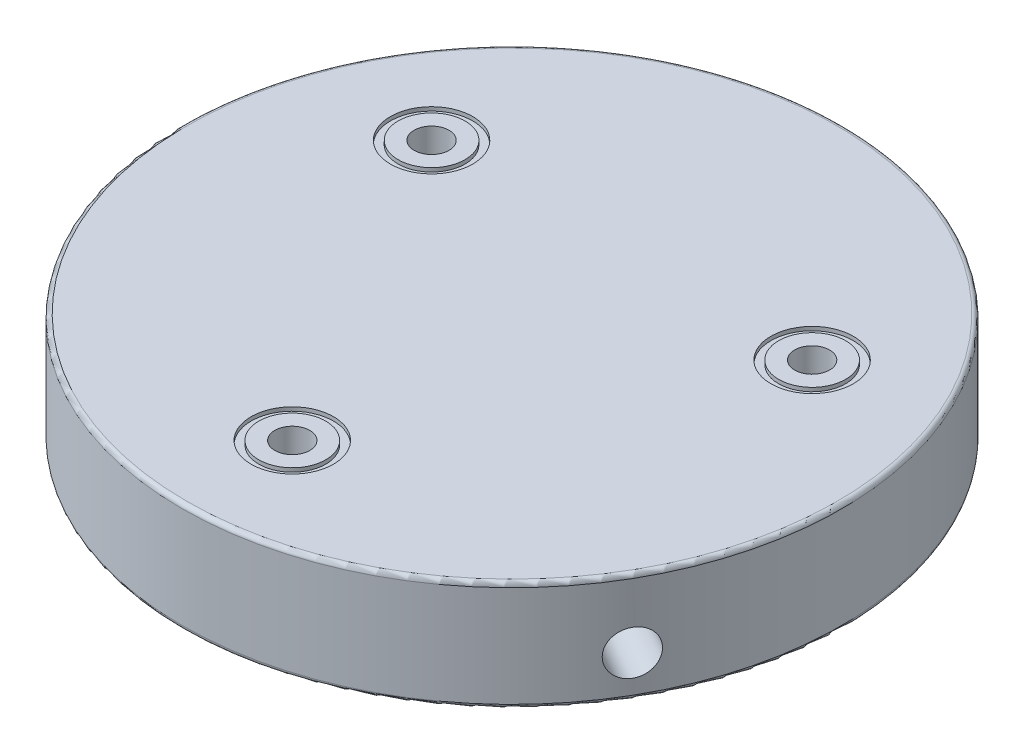
SolidWorks part; units mm, degrees
ref_plane "Front Plane" through (0, 0, 0) normal (0, 0, 1) x (1, 0, 0)
ref_plane "Top Plane" through (0, 0, 0) normal (0, 1, 0) x (1, 0, 0)
ref_plane "Right Plane" through (0, 0, 0) normal (1, 0, 0) x (0, 0, -1)
sketch "Sketch1" plane through (0, 0, 0) normal (0, 1, 0) x (1, 0, 0)
  circle A0 centre (0, 0) radius 38.1
  dimension "D1" = 76.2
extrude "Boss-Extrude1" add sketch "Sketch1" along normal blind 12.7
sketch "Sketch2" plane through (0, 0, 0) normal (0, -1, 0) x (1, 0, 0)
  circle A0 centre (0, 0) radius 15.875
  dimension "D1" = 31.75
extrude "Cut-Extrude1" cut sketch "Sketch2" against normal blind 9.525
sketch "Sketch3" plane through (0, 0, 0) normal (0, -1, 0) x (1, 0, 0)
  circle A0 centre (0, 25.4) radius 2.0193
  dimension "D1" = 4.0386
  dimension "D2" = 25.4
extrude "Cut-Extrude2" cut sketch "Sketch3" against normal up to next (12.7 mm away)
pattern_circular "CirPattern1" count 3 over 360 about axis through (0, 0, 0) along (0, 1, 0) of "Cut-Extrude2"
sketch "Sketch4" plane through (0, 0, 0) normal (0, 0, 1) x (1, 0, 0)
  circle A0 centre (0, 4.7625) radius 2.5527
  dimension "D1" = 5.1054
  dimension "D2" = 4.7625
extrude "Cut-Extrude3" cut sketch "Sketch4" against normal up to next
pattern_circular "CirPattern2" count 3 over 360 about axis through (0, 0, 0) along (0, 1, 0) of "Cut-Extrude3"
fillet "Fillet1" radius 0.508 3 edges at (0, 0, 38.1) (0, 12.7, 38.1) (0, 0, -15.875)
sketch "Sketch5" plane through (0, 12.7, 0) normal (0, 1, 0) x (1, 0, 0)
  circle A0 centre (0, -25.4) radius 3.8735
  circle A1 centre (0, -25.4) radius 4.7625
  dimension "D1" = 9.525
  dimension "D2" = 7.747
extrude "Cut-Extrude4" cut sketch "Sketch5" against normal blind 0.4445
pattern_circular "CirPattern3" count 3 over 360 about axis through (0, 0, 0) along (0, 1, 0) of "Cut-Extrude4"
